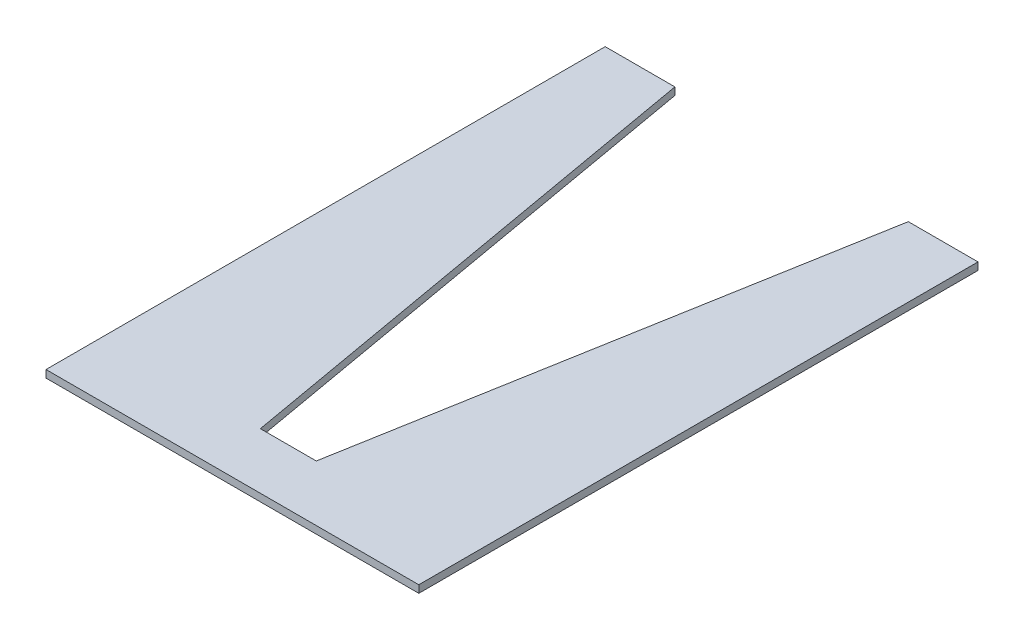
SolidWorks part; units mm, degrees
material "Cedar"
ref_plane "Front Plane" through (0, 0, 0) normal (0, 0, 1) x (1, 0, 0)
ref_plane "Top Plane" through (0, 0, 0) normal (0, 1, 0) x (1, 0, 0)
ref_plane "Right Plane" through (0, 0, 0) normal (1, 0, 0) x (0, 0, -1)
sketch "Sketch1" plane through (0, 0, 0) normal (0, 1, 0) x (1, 0, 0)
  line L0 (-100, 292.4393) -> (-100, -7.5607)
  line L1 (-100, -7.5607) -> (100, -7.5607)
  line L2 (100, -7.5607) -> (100, 292.4393)
  line L3 (100, 292.4393) -> (62.6083, 292.4393)
  line L4 (62.6083, 292.4393) -> (15, 22.4393)
  line L5 (15, 22.4393) -> (-15, 22.4393)
  line L6 (-15, 22.4393) -> (-62.6083, 292.4393)
  line L7 (-62.6083, 292.4393) -> (-100, 292.4393)
  line L8 (0, 18.2292) -> (0, -7.5607) construction
  dimension "D1" = 30
  dimension "D2" = 200
  dimension "D3" = 300
  dimension "D4" = 10
  dimension "D5" = 30
extrude "Boss-Extrude1" add sketch "Sketch1" along normal blind 4 contours L6 L7 L0 L1 L2 L3 L4 L5
